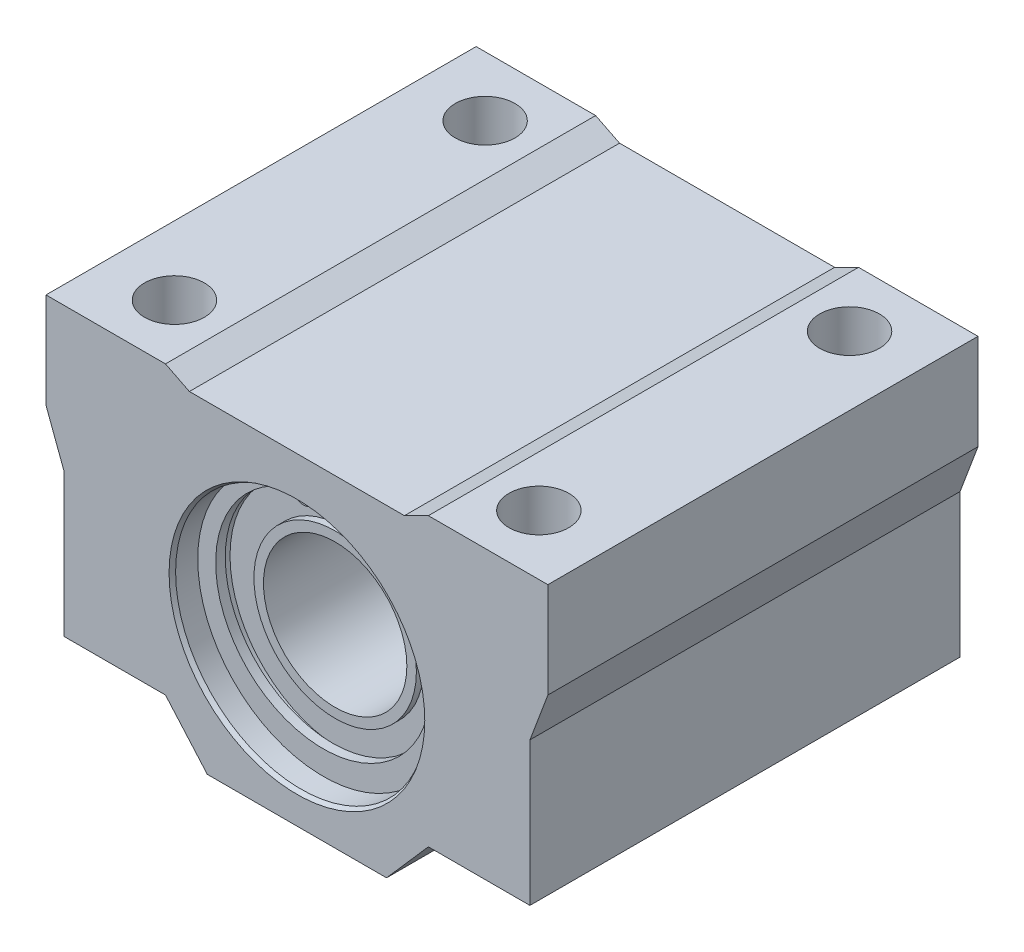
SolidWorks part; units mm, degrees
material "1060 Alloy"
ref_plane "Front Plane" through (0, 0, 0) normal (0, 0, 1) x (1, 0, 0)
ref_plane "Top Plane" through (0, 0, 0) normal (0, 1, 0) x (1, 0, 0)
ref_plane "Right Plane" through (0, 0, 0) normal (1, 0, 0) x (0, 0, -1)
sketch "Sketch1" plane through (0, 0, 0) normal (0, 0, 1) x (1, 0, 0)
  line L0 (0, 0) -> (0, -120.6263) construction
  line L1 (-9, -1) -> (9, -1)
  line L2 (9, -1) -> (11, 0)
  line L3 (11, 0) -> (21, 0)
  line L4 (21, 0) -> (21, -8)
  line L5 (21, -8) -> (19.5, -12)
  line L6 (19.5, -12) -> (19.5, -24)
  line L7 (19.5, -24) -> (11, -24)
  line L8 (11, -24) -> (7.5, -28)
  line L9 (7.5, -28) -> (-7.5, -28)
  line L10 (-19.5, -12) -> (-19.5, -24)
  line L11 (-21, -8) -> (-19.5, -12)
  line L12 (-21, 0) -> (-21, -8)
  line L13 (-11, 0) -> (-21, 0)
  line L14 (-9, -1) -> (-11, 0)
  line L15 (-19.5, -24) -> (-11, -24)
  line L16 (-11, -24) -> (-7.5, -28)
  circle A0 centre (0, -15) radius 10.5
  point P19 (0, -1)
  point P21 (0, -28)
  dimension "D4" = 21
  dimension "D1" = 8
  dimension "D2" = 1
  dimension "D3" = 1.5
  dimension "D5" = 42
  dimension "D6" = 28
  dimension "D7" = 12
  dimension "D8" = 2
  dimension "D9" = 24
  dimension "D10" = 15
  dimension "D11" = 10
  dimension "D12" = 15
  dimension "D13" = 22
extrude "Boss-Extrude1" add sketch "Sketch1" along normal mid plane 36
sketch "Sketch2" plane through (0, 0, 0) normal (1, 0, 0) x (0, 0, -1)
  line L0 (-30.2753, -15) -> (18, -15) construction
  line L1 (18, -25.5) -> (18, -4.5) construction
  line L2 (18, -25.5) -> (18, -4.5) construction
  line L3 (0, 0) -> (0, -32.2949) construction
  line L4 (-15, -4.5) -> (15, -4.5)
  line L5 (15, -4.5) -> (15, -5.6)
  line L6 (15, -5.6) -> (14.2, -5.6)
  line L7 (14.2, -5.6) -> (14.2, -8.2)
  line L8 (14.2, -8.2) -> (14.8, -8.2)
  line L9 (14.8, -8.2) -> (14.8, -9)
  line L10 (14.8, -9) -> (-14.8, -9)
  line L11 (-14.8, -8.2) -> (-14.8, -9)
  line L12 (-14.2, -8.2) -> (-14.8, -8.2)
  line L13 (-14.2, -5.6) -> (-14.2, -8.2)
  line L14 (-15, -5.6) -> (-14.2, -5.6)
  line L15 (-15, -4.5) -> (-15, -5.6)
  line L16 (14.8, -21) -> (-14.8, -21) construction
  line L17 (-15, -25.5) -> (15, -25.5) construction
  point P16 (0, -9)
  point P21 (0, -4.5)
  dimension "D1" = 1.1
  dimension "D2" = 0.8
  dimension "D3" = 21
  dimension "D4" = 12
  dimension "D5" = 30
  dimension "D6" = 0.8
  dimension "D7" = 0.6
revolve "Revolve1" add sketch "Sketch2" angle 360 about L0
sketch "Sketch3" plane through (0, 0, 15) normal (0, 0, 1) x (1, 0, 0)
  line L0 (0, 4.2304) -> (0, -35.7092) construction
  line L1 (1.1412, -4.0594) -> (0.783, -5.5346)
  line L2 (-1.1412, -4.0594) -> (-0.783, -5.5346)
  circle A0 centre (1.6627, -5.7482) radius 0.4873
  circle A1 centre (0, -15) radius 9.4 construction
  arc A2 (0.783, -5.5346) -> (2.5594, -5.8716) centre (1.6627, -5.7482) ccw
  arc A3 (1.1412, -4.0594) -> (-1.1412, -4.0594) centre (0, -15) cw
  arc A4 (2.5594, -5.8716) -> (-2.5594, -5.8716) centre (0, -14.5) cw
  circle A5 centre (-1.6627, -5.7482) radius 0.4873
  arc A6 (-0.783, -5.5346) -> (-2.5594, -5.8716) centre (-1.6627, -5.7482) cw
  dimension "D1" = 11
  dimension "D3" = 9
  dimension "D2" = 0.5
extrude "Boss-Extrude2" add sketch "Sketch3" along normal blind 0.8
mirror "Mirror1" about plane through (0, 0, 0) normal (0, 0, 1) of "Boss-Extrude2"
hole_wizard "M5 Tapped Hole1" positions "Sketch5" profile "Sketch6" tap size "M5" standard "DIN" end condition through all
sketch "Sketch5" plane through (0, 0, 0) normal (0, 1, 0) x (1, 0, 0)
  line L0 (0, 19.7581) -> (0, 0) construction
  line L1 (0, 0) -> (23.7777, 0) construction
  point P6 (15.25, 13)
  point P10 (15.25, -13)
  point P12 (-15.25, 13)
  point P13 (-15.25, -13)
  dimension "D1" = 30.5
  dimension "D2" = 26
sketch "Sketch6" plane through (15.25, 0, -13) normal (1, 0, 0) x (0, 0, 1)
  line L0 (0, 0) -> (0, 24)
  line L1 (2.1, 23.6) -> (2.5, 24)
  line L2 (2.1, 23.6) -> (2.1, 12)
  line L3 (2.1, 12) -> (2.5, 12)
  line L4 (2.5, 12) -> (2.5, 0)
  line L5 (2.5, 0) -> (0, 0)
  line L11 (0, -6.35) -> (0, 107.95) construction
  line L12 (2.5, 24) -> (0, 24)
  line L13 (-2.1, 23.6) -> (-2.5, 24) construction
  dimension "Thru Tap Drill Dia." = 4.2
  dimension "Thru Tap Drill Depth" = 24
  dimension "Thread Major Dia." = 5
  dimension "Thread Depth" = 12
  dimension "Far C'Sink Dia." = 5
  dimension "Far C'Sink Angle" = 90
chamfer "Chamfer1" distance 0.2 angle 60 2 edges at (10.5, -15, -18) (10.5, -15, 18)
